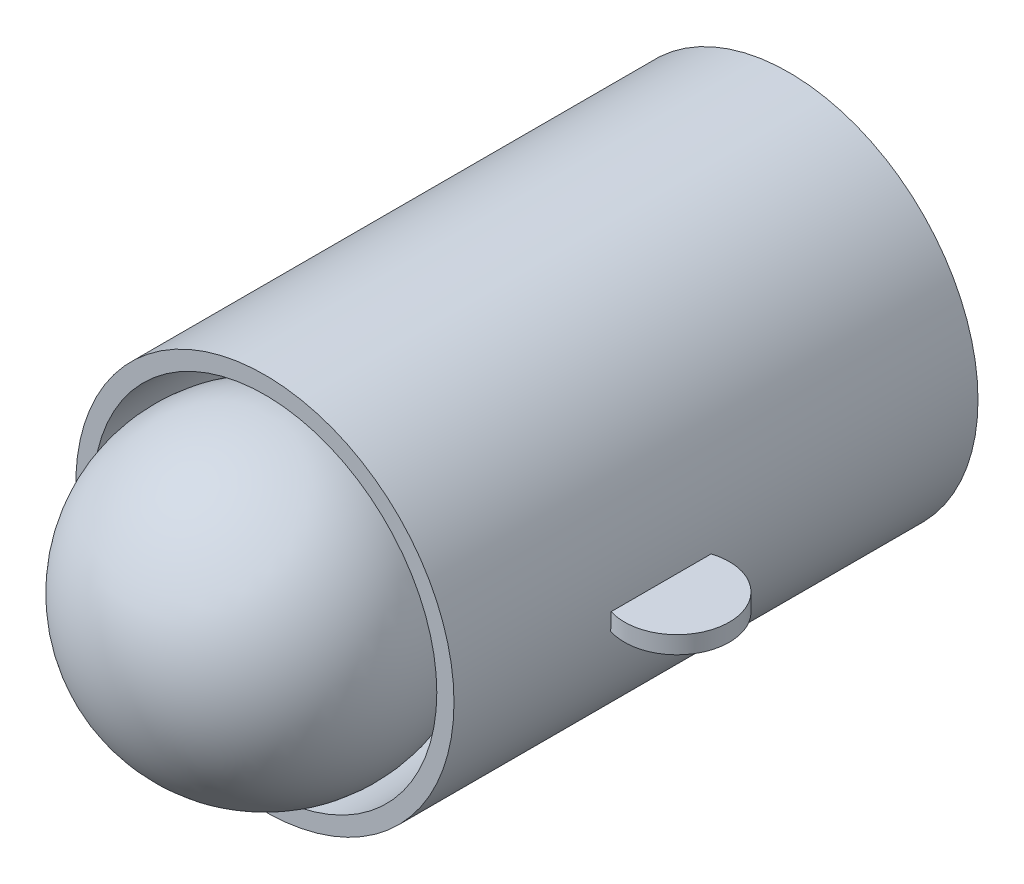
SolidWorks part; units mm, degrees
ref_plane "Front Plane" through (0, 0, 0) normal (0, 0, 1) x (1, 0, 0)
ref_plane "Top Plane" through (0, 0, 0) normal (0, 1, 0) x (1, 0, 0)
ref_plane "Right Plane" through (0, 0, 0) normal (1, 0, 0) x (0, 0, -1)
sketch "Sketch1" plane through (0, 0, 0) normal (0, 0, 1) x (1, 0, 0)
  line L0 (0, 27.5) -> (0, -27.5) construction
  circle A0 centre (0, 0) radius 27.5
  point P5 (-286.191, -49.6964)
  point P6 (-286.191, -70.2573)
  dimension "D1" = 55
extrude "Boss-Extrude1" add sketch "Sketch1" along normal blind 76.2
sketch "Sketch2" plane through (0, 0, 76.2) normal (0, 0, 1) x (1, 0, 0)
  line L0 (22.975, 27.3906) -> (23.1124, 27.8637) construction
  line L1 (23.1124, 27.8637) -> (-22.9427, 27.8637) construction
  circle A0 centre (0, 0) radius 25
  dimension "D1" = 50
extrude "Cut-Extrude1" cut sketch "Sketch2" against normal blind 76.2
sketch "Sketch3" plane through (0, 0, 76.2) normal (0, 0, 1) x (1, 0, 0)
  line L0 (0, 27.5) -> (0, -27.5) construction
  line L1 (-25, 0) -> (25, 0) construction
  line L2 (0, 20) -> (0, -20) construction
  circle A0 centre (0, 0) radius 27.5 construction
  circle A1 centre (0, 0) radius 25 construction
  arc A2 (0, -20) -> (0, 20) centre (0, 0) ccw
  point P10 (25, 0)
  point P12 (20, 0)
  point P13 (27.5, 0)
  point P14 (37.66, 0)
  dimension "D1" = 40
  dimension "D2" = 7.5
  dimension "D3" = 10.16
revolve "Revolve-Thin1" add sketch "Sketch3" angle 360 about L0
sketch "Sketch5" plane through (0, 0, 76.2) normal (0, 0, 1) x (1, 0, 0)
  line L0 (0, 27.5) -> (0, -27.5) construction
  line L1 (-27.5, 0) -> (27.5, 0) construction
  circle A0 centre (0, 0) radius 27.5 construction
  point P8 (37.5703, 0)
  point P9 (22.3303, 0)
  dimension "D1" = 15.24
  dimension "D2" = 5.1697
ref_plane "Plane3" through (0, 0, 0) normal (0, -1, 0) x (-1, 0, 0)
sketch "Sketch6" plane through (0, 0, 0) normal (0, -1, 0) x (-1, 0, 0)
  line L0 (-27.5, 0) -> (-27.5, -76.2) construction
  circle A0 centre (-29.7933, -46.0733) radius 7.62
  point P2 (-31.1362, -40.9273)
  point P3 (-22.1733, -46.0733)
  point P4 (-37.4133, -46.0733)
  point P5 (-27.5, -76.2)
  point P8 (-27.5, -53.34)
  dimension "D1" = 15.24
  dimension "D2" = 22.86
extrude "Boss-Extrude3" add sketch "Sketch6" along normal blind 2.54 contours A0
